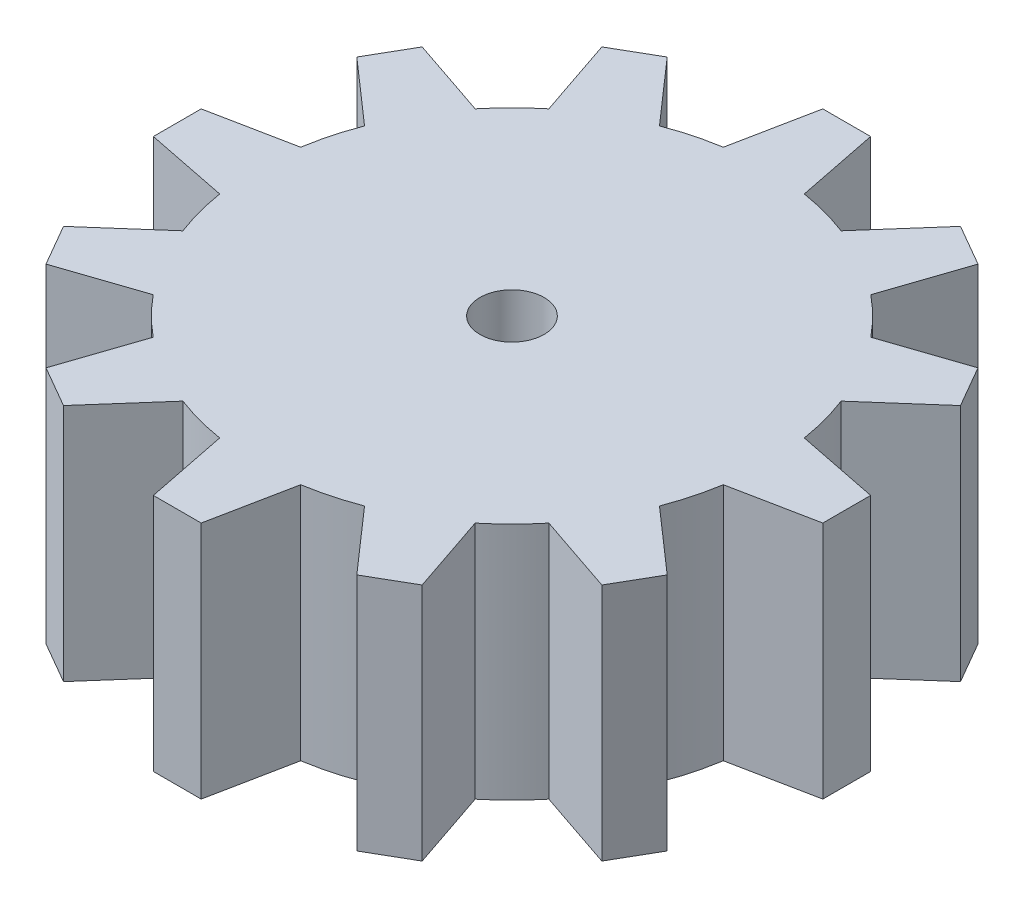
SolidWorks part; units mm, degrees
ref_plane "Front Plane" through (0, 0, 0) normal (0, 0, 1) x (1, 0, 0)
ref_plane "Top Plane" through (0, 0, 0) normal (0, 1, 0) x (1, 0, 0)
ref_plane "Right Plane" through (0, 0, 0) normal (1, 0, 0) x (0, 0, -1)
sketch "Sketch1" plane through (0, 0, 0) normal (0, 1, 0) x (1, 0, 0)
  line L0 (-2.5406, 15.797) -> (-1.5, 21)
  line L1 (2.5406, 15.797) -> (1.5, 21)
  line L2 (-1.5, 21) -> (1.5, 21)
  line L3 (10.0987, 12.4103) -> (11.799, 17.4365)
  line L4 (9.201, 18.9365) -> (11.799, 17.4365)
  line L5 (5.6983, 14.9509) -> (9.201, 18.9365)
  line L6 (14.9509, 5.6983) -> (18.9365, 9.201)
  line L7 (17.4365, 11.799) -> (18.9365, 9.201)
  line L8 (12.4103, 10.0987) -> (17.4365, 11.799)
  line L9 (15.797, -2.5406) -> (21, -1.5)
  line L10 (21, 1.5) -> (21, -1.5)
  line L11 (15.797, 2.5406) -> (21, 1.5)
  line L12 (12.4103, -10.0987) -> (17.4365, -11.799)
  line L13 (18.9365, -9.201) -> (17.4365, -11.799)
  line L14 (14.9509, -5.6983) -> (18.9365, -9.201)
  line L15 (5.6983, -14.9509) -> (9.201, -18.9365)
  line L16 (11.799, -17.4365) -> (9.201, -18.9365)
  line L17 (10.0987, -12.4103) -> (11.799, -17.4365)
  line L18 (-2.5406, -15.797) -> (-1.5, -21)
  line L19 (1.5, -21) -> (-1.5, -21)
  line L20 (2.5406, -15.797) -> (1.5, -21)
  line L21 (-10.0987, -12.4103) -> (-11.799, -17.4365)
  line L22 (-9.201, -18.9365) -> (-11.799, -17.4365)
  line L23 (-5.6983, -14.9509) -> (-9.201, -18.9365)
  line L24 (-14.9509, -5.6983) -> (-18.9365, -9.201)
  line L25 (-17.4365, -11.799) -> (-18.9365, -9.201)
  line L26 (-12.4103, -10.0987) -> (-17.4365, -11.799)
  line L27 (-15.797, 2.5406) -> (-21, 1.5)
  line L28 (-21, -1.5) -> (-21, 1.5)
  line L29 (-15.797, -2.5406) -> (-21, -1.5)
  line L30 (-12.4103, 10.0987) -> (-17.4365, 11.799)
  line L31 (-18.9365, 9.201) -> (-17.4365, 11.799)
  line L32 (-14.9509, 5.6983) -> (-18.9365, 9.201)
  line L33 (-5.6983, 14.9509) -> (-9.201, 18.9365)
  line L34 (-11.799, 17.4365) -> (-9.201, 18.9365)
  line L35 (-10.0987, 12.4103) -> (-11.799, 17.4365)
  arc A0 (-2.5406, 15.797) -> (-5.6983, 14.9509) centre (0, 0) ccw
  arc A1 (-10.0987, 12.4103) -> (-12.4103, 10.0987) centre (0, 0) ccw
  arc A2 (-14.9509, 5.6983) -> (-15.797, 2.5406) centre (0, 0) ccw
  arc A3 (-15.797, -2.5406) -> (-14.9509, -5.6983) centre (0, 0) ccw
  arc A4 (5.6983, 14.9509) -> (2.5406, 15.797) centre (0, 0) ccw
  arc A5 (12.4103, 10.0987) -> (10.0987, 12.4103) centre (0, 0) ccw
  arc A6 (15.797, 2.5406) -> (14.9509, 5.6983) centre (0, 0) ccw
  arc A7 (14.9509, -5.6983) -> (15.797, -2.5406) centre (0, 0) ccw
  arc A8 (10.0987, -12.4103) -> (12.4103, -10.0987) centre (0, 0) ccw
  arc A9 (2.5406, -15.797) -> (5.6983, -14.9509) centre (0, 0) ccw
  arc A10 (-5.6983, -14.9509) -> (-2.5406, -15.797) centre (0, 0) ccw
  arc A11 (-12.4103, -10.0987) -> (-10.0987, -12.4103) centre (0, 0) ccw
  point P2 (0, 16)
extrude "Boss-Extrude1" add sketch "Sketch1" along normal blind 15
sketch "Sketch2" plane through (0, 0, 0) normal (0, 1, 0) x (1, 0, 0)
  circle A0 centre (0, 0) radius 2.0131
extrude "Cut-Extrude1" cut sketch "Sketch2" along normal up to next
sketch "Sketch3" plane through (0, 15, 0) normal (0, 1, 0) x (1, 0, 0)
  circle A2 centre (0, 0) radius 14
  dimension "D1" = 28
